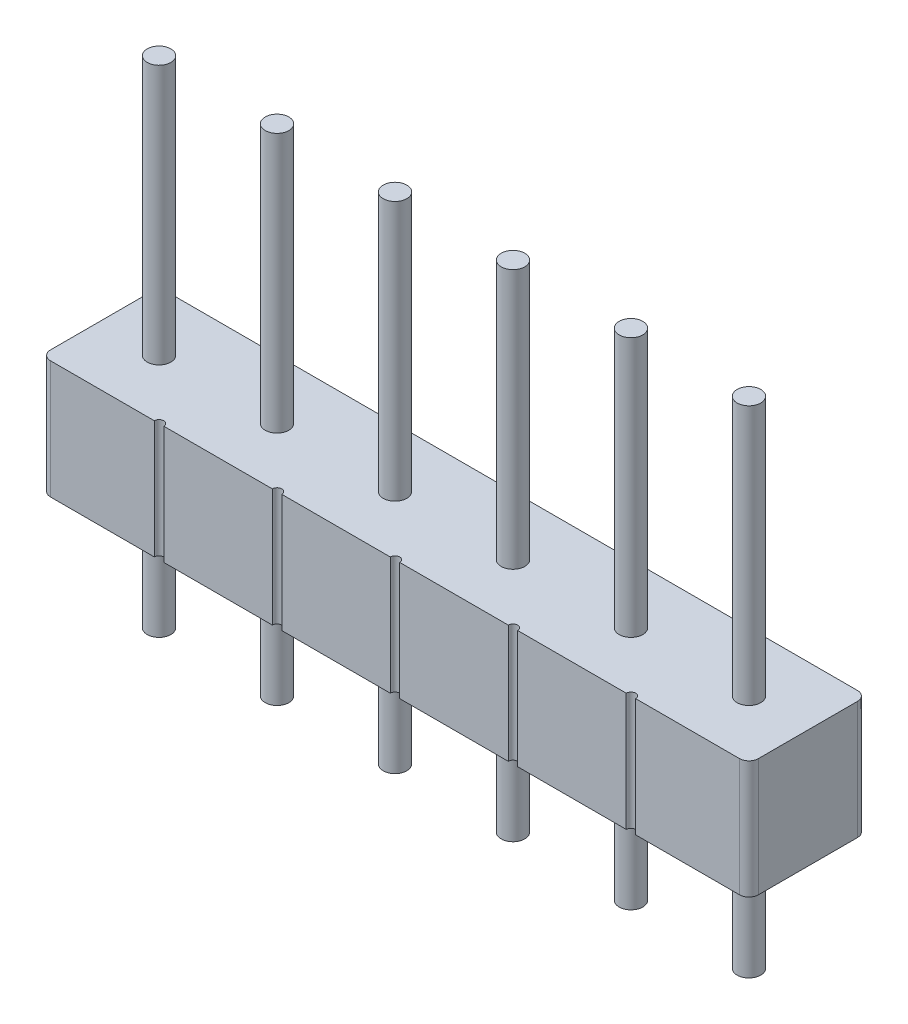
SolidWorks part; units mm, degrees
ref_plane "Ön Düzlem" through (0, 0, 0) normal (0, 0, 1) x (1, 0, 0)
ref_plane "Üst Düzlem" through (0, 0, 0) normal (0, 1, 0) x (1, 0, 0)
ref_plane "Sağ Düzlem" through (0, 0, 0) normal (1, 0, 0) x (0, 0, -1)
sketch "Çizim1" plane through (0, 0, 0) normal (0, 1, 0) x (1, 0, 0)
  line L1 (-7.3, 1.25) -> (-5.1, 1.25)
  line L2 (-7.5, 1.05) -> (-7.5, -1.05)
  line L3 (-7.3, -1.25) -> (-5.1, -1.25)
  line L4 (7.5, 1.05) -> (7.5, -1.05)
  line L5 (-7.5, 1.25) -> (7.5, -1.25) construction
  line L6 (-7.5, -1.25) -> (7.5, 1.25) construction
  line L7 (-7.5, 0) -> (7.5, 0) construction
  line L13 (-4.9, 1.25) -> (-2.6, 1.25)
  line L14 (-2.4, 1.25) -> (-0.1, 1.25)
  line L15 (0.1, 1.25) -> (2.4, 1.25)
  line L16 (2.6, 1.25) -> (4.9, 1.25)
  line L17 (5.1, 1.25) -> (7.3, 1.25)
  line L18 (5.1, -1.25) -> (7.3, -1.25)
  line L19 (2.6, -1.25) -> (4.9, -1.25)
  line L20 (0.1, -1.25) -> (2.4, -1.25)
  line L21 (-2.4, -1.25) -> (-0.1, -1.25)
  line L22 (-4.9, -1.25) -> (-2.6, -1.25)
  circle A0 centre (-1.25, 0) radius 0.25
  circle A1 centre (-3.75, 0) radius 0.25
  circle A2 centre (-6.25, 0) radius 0.25
  circle A3 centre (6.25, 0) radius 0.25
  circle A4 centre (3.75, 0) radius 0.25
  circle A5 centre (1.25, 0) radius 0.25
  arc A6 (-5.1, 1.25) -> (-4.9, 1.25) centre (-5, 1.25) ccw
  arc A7 (-2.6, 1.25) -> (-2.4, 1.25) centre (-2.5, 1.25) ccw
  arc A8 (-0.1, 1.25) -> (0.1, 1.25) centre (0, 1.25) ccw
  arc A9 (0.1, -1.25) -> (-0.1, -1.25) centre (0, -1.25) ccw
  arc A10 (-2.4, -1.25) -> (-2.6, -1.25) centre (-2.5, -1.25) ccw
  arc A11 (-4.9, -1.25) -> (-5.1, -1.25) centre (-5, -1.25) ccw
  arc A12 (2.4, -1.25) -> (2.6, -1.25) centre (2.5, -1.25) cw
  arc A13 (4.9, -1.25) -> (5.1, -1.25) centre (5, -1.25) cw
  arc A14 (2.6, 1.25) -> (2.4, 1.25) centre (2.5, 1.25) cw
  arc A15 (5.1, 1.25) -> (4.9, 1.25) centre (5, 1.25) cw
  arc A16 (7.3, -1.25) -> (7.5, -1.05) centre (7.3, -1.05) ccw
  arc A17 (7.3, 1.25) -> (7.5, 1.05) centre (7.3, 1.05) cw
  arc A18 (-7.5, -1.05) -> (-7.3, -1.25) centre (-7.3, -1.05) ccw
  arc A19 (-7.3, 1.25) -> (-7.5, 1.05) centre (-7.3, 1.05) ccw
  point P0 (0, 0)
  dimension "D3" = 0.5
  dimension "D5" = 2.5
  dimension "D6" = 2.5
  dimension "D9" = 0.2
  dimension "D10" = 0.2
  dimension "D1" = 15
  dimension "D2" = 2.5
extrude "Yükseklik-Ekstrüzyon1" add sketch "Çizim1" along normal blind 2.5
sketch "Çizim2" plane through (0, 2.5, 0) normal (0, 1, 0) x (1, 0, 0)
  circle A0 centre (-6.25, 0) radius 0.25
  circle A1 centre (-3.75, 0) radius 0.25
  circle A2 centre (-1.25, 0) radius 0.25
  circle A3 centre (1.25, 0) radius 0.25
  circle A4 centre (3.75, 0) radius 0.25
  circle A5 centre (6.25, 0) radius 0.25
extrude "Yükseklik-Ekstrüzyon2" add sketch "Çizim2" along normal blind 5.5 and the other way blind 5
